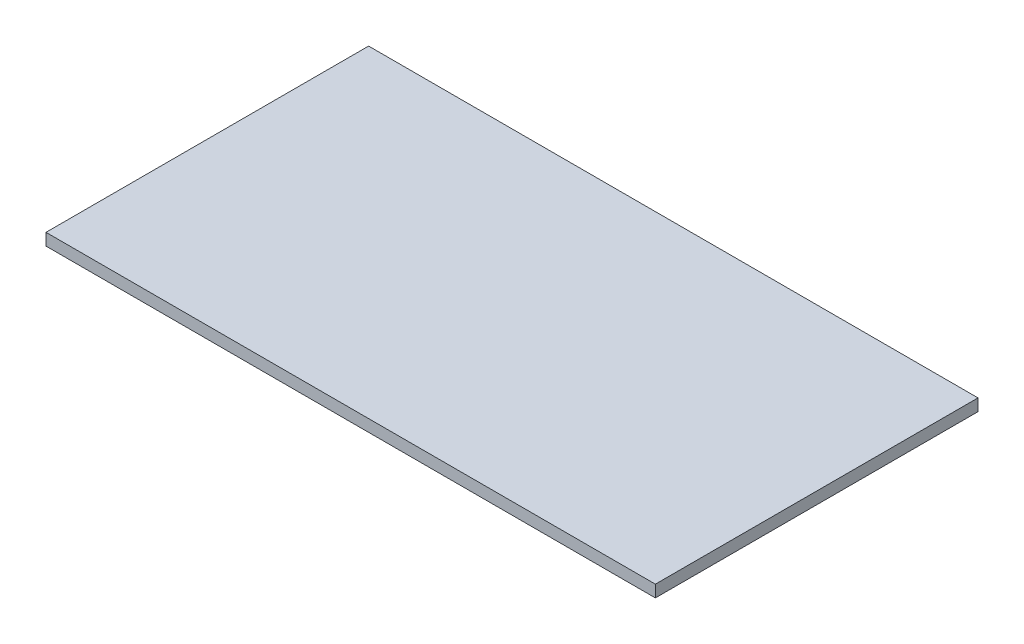
SolidWorks part; units mm, degrees
material "Beech"
ref_plane "Front" through (0, 0, 0) normal (0, 0, 1) x (1, 0, 0)
ref_plane "Top" through (0, 0, 0) normal (0, 1, 0) x (1, 0, 0)
ref_plane "Right" through (0, 0, 0) normal (1, 0, 0) x (0, 0, -1)
sketch "Sketch1" plane through (0, 0, 0) normal (0, 1, 0) x (1, 0, 0)
  line L1 (-255, -135) -> (255, -135)
  line L2 (-255, -135) -> (-255, 135)
  line L3 (-255, 135) -> (255, 135)
  line L4 (255, -135) -> (255, 135)
  line L5 (-255, -135) -> (255, 135) construction
  line L6 (-255, 135) -> (255, -135) construction
  point P0 (0, 0)
  dimension "D1" = 270
  dimension "D2" = 510
extrude "Boss-Extrude1" add sketch "Sketch1" along normal blind 10
